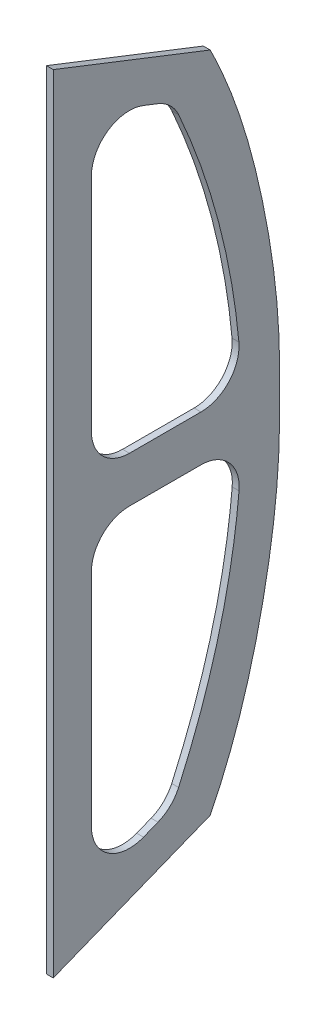
SolidWorks part; units mm, degrees
ref_plane "Спереди" through (0, 0, 0) normal (0, 0, 1) x (1, 0, 0)
ref_plane "Сверху" through (0, 0, 0) normal (0, 1, 0) x (1, 0, 0)
ref_plane "Справа" through (0, 0, 0) normal (1, 0, 0) x (0, 0, -1)
sketch "Эскиз1" plane through (0, 0, 0) normal (1, 0, 0) x (0, 0, -1)
  line L0 (-455, -523) -> (-455, 523) construction
  line L1 (-243, -438.6617) -> (-243, 440) construction
  line L2 (-455, -516.5426) -> (-455, 516.5565)
  line L3 (-455, 516.5565) -> (-249, 435.9056)
  line L4 (-455, -516.5426) -> (-249, -434.5913)
  line L5 (-449, 514.2075) -> (-249, 435.9056) construction
  line L6 (-449, -514.1557) -> (-449, 514.2075) construction
  line L7 (-449, -514.1557) -> (-249, -434.5913) construction
  line L8 (-455, -523) -> (-243, -438.6617) construction
  line L9 (-249, -434.5913) -> (-249, 435.9056) construction
  line L10 (-455, 523) -> (-243, 440) construction
  line L11 (-405, -369.1378) -> (-405, -79.8338)
  line L12 (-336.7718, 416.5736) -> (-317.8152, 409.152)
  line L13 (-336.5177, -415.5965) -> (-317.5281, -408.042)
  line L14 (-405, 80.2227) -> (-405, 370.0147)
  line L15 (-355, 30.2227) -> (-261.0428, 30.2227)
  line L16 (-260.7875, -29.9401) -> (-354.9436, -29.8338)
  line L17 (-405, -442.8402) -> (-405, 443.2856) construction
  line L18 (-249, 435.9056) -> (-249, -434.5913) construction
  line L19 (-299, 401.7856) -> (-299, -400.6711) construction
  line L20 (-405, 443.2856) -> (-299, 401.7856) construction
  line L21 (-405, -442.8402) -> (-299, -400.6711) construction
  arc A0 (-405, -79.8338) -> (-354.9436, -29.8338) centre (-355, -79.8338) cw
  arc A1 (-405, 80.2227) -> (-355, 30.2227) centre (-355, 80.2227) ccw
  arc A2 (-211.0524, -84.5016) -> (-260.7875, -29.9401) centre (-260.8439, -79.94) ccw
  arc A3 (-211.259, 84.8675) -> (-261.0428, 30.2227) centre (-261.0428, 80.2227) cw
  arc A4 (-290.3777, 382.9557) -> (-317.8152, 409.152) centre (-336.0434, 362.5931) ccw
  arc A5 (-336.7718, 416.5736) -> (-405, 370.0147) centre (-355, 370.0147) ccw
  arc A6 (-336.5177, -415.5965) -> (-405, -369.1378) centre (-355, -369.1378) cw
  arc A7 (-317.5281, -408.042) -> (-290.4195, -382.1132) centre (-336.0104, -361.5834) ccw
  spline S0 degree 3 poles (-290.3777, 382.9557) (-270.1515, 337.5962) (-234.7903, 239.4884) (-216.3117, 139.0234) (-211.259, 84.8675) knots 0.024188 0.024188 0.024188 0.024188 0.198717 0.397434 0.397434 0.397434 0.397434
  spline S1 degree 3 poles (-211.0524, -84.5016) (-216.0027, -138.5366) (-234.4319, -238.8485) (-270.0115, -336.7929) (-290.4195, -382.1132) knots 0.603423 0.603423 0.603423 0.603423 0.801711 0.976153 0.976153 0.976153 0.976153
  spline S2 degree 3 poles (-249, 435.9056) (-244.8122, 427.5807) (-236.8014, 410.7383) (-222.2124, 376.4639) (-206.4721, 332.5736) (-191.0652, 278.6225) (-178.6184, 223.742) (-168.6012, 168.3762) (-162.6642, 121.9958) (-159.5885, 84.7804) (-158.191, 56.8473) (-157.6991, 28.8204) (-157.6682, 0.6571) (-157.6991, -27.5061) (-158.191, -55.533) (-159.5885, -83.4661) (-162.6642, -120.6815) (-168.6012, -167.0619) (-178.6184, -222.4277) (-191.0652, -277.3082) (-206.4721, -331.2593) (-222.2124, -375.1496) (-236.8014, -409.424) (-244.8122, -426.2664) (-249, -434.5913) knots 0.002534 0.002534 0.002534 0.002534 0.033626 0.064718 0.126901 0.189084 0.251267 0.31345 0.375634 0.406725 0.437817 0.468908 0.5 0.531092 0.562183 0.593275 0.624366 0.68655 0.748733 0.810916 0.873099 0.935282 0.966374 0.997466 0.997466 0.997466 0.997466
  dimension "D3" = 50
  dimension "D4" = 50
  dimension "D5" = 50
  dimension "D6" = 50
  dimension "D7" = 50
  dimension "D8" = 50
  dimension "D9" = 50
  dimension "D10" = 50
  dimension "D1" = 6
  dimension "D2" = 50
extrude "Бобышка-Вытянуть4" add sketch "Эскиз1" along normal blind 9
